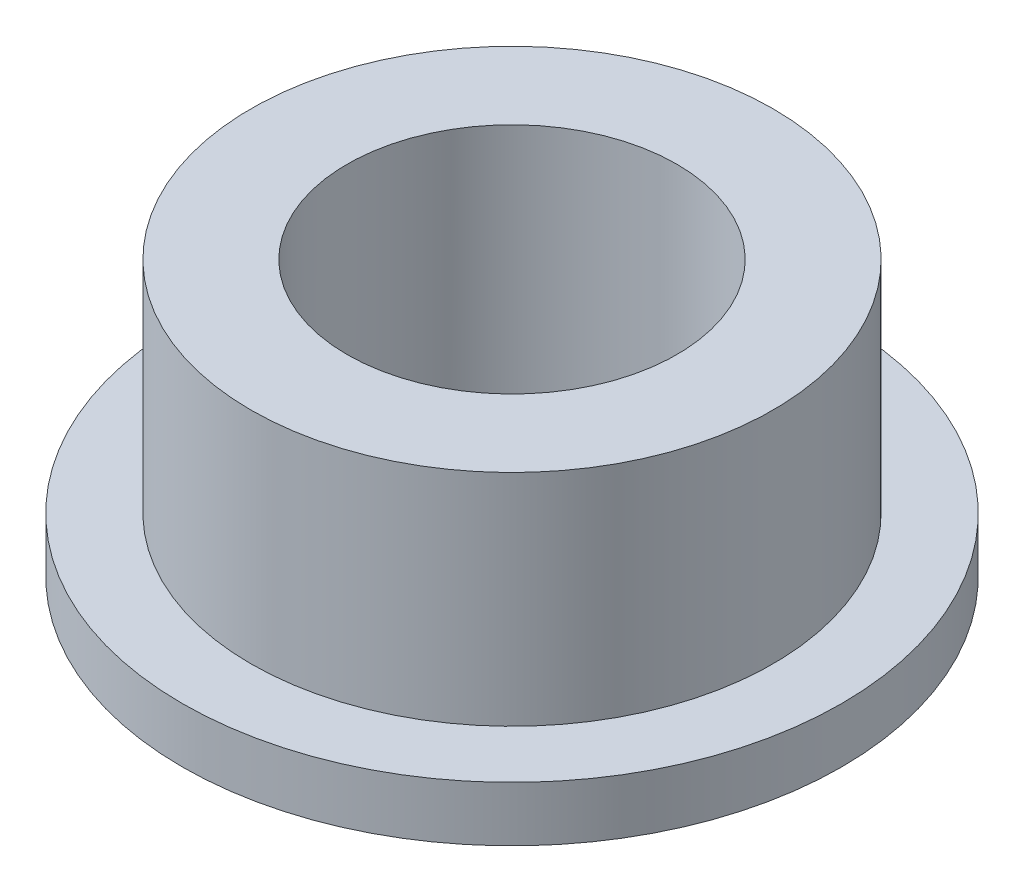
SolidWorks part; units mm, degrees
ref_plane "Front Plane" through (0, 0, 0) normal (0, 0, 1) x (1, 0, 0)
ref_plane "Top Plane" through (0, 0, 0) normal (0, 1, 0) x (1, 0, 0)
ref_plane "Right Plane" through (0, 0, 0) normal (1, 0, 0) x (0, 0, -1)
sketch "Sketch1" plane through (0, 0, 0) normal (0, 1, 0) x (1, 0, 0)
  circle A0 centre (0, 0) radius 4.75
  circle A1 centre (0, 0) radius 3.001
  dimension "D1" = 9.5
  dimension "D2" = 6.002
extrude "Boss-Extrude1" add sketch "Sketch1" along normal blind 4
sketch "Sketch2" plane through (0, 0, 0) normal (0, -1, 0) x (1, 0, 0)
  circle A0 centre (0, 0) radius 6
  circle A1 centre (0, 0) radius 3.001 construction
  circle A2 centre (0, 0) radius 3.001
  dimension "D1" = 12
extrude "Boss-Extrude2" add sketch "Sketch2" along normal blind 1
scale "Scale1" scale about centroid uniform scaling yes scale factor 1.5
